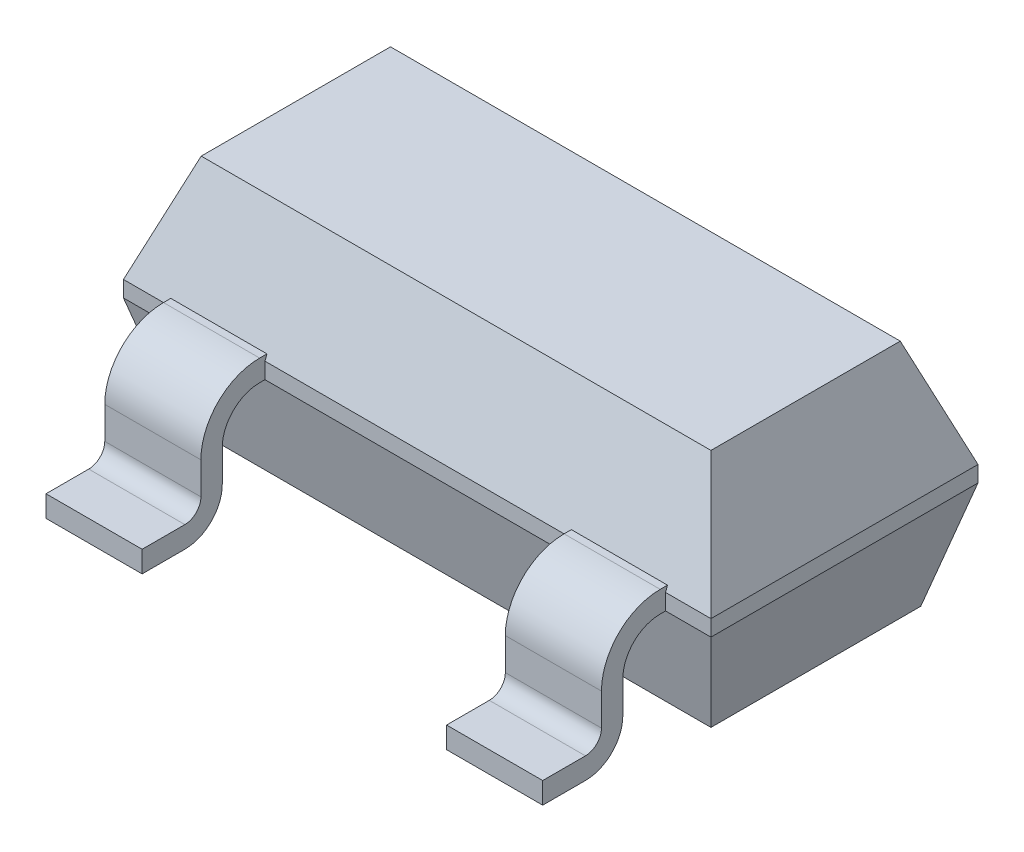
SolidWorks part; units mm, degrees
ref_plane "Front Plane" through (0, 0, 0) normal (0, 0, 1) x (1, 0, 0)
ref_plane "Top Plane" through (0, 0, 0) normal (0, 1, 0) x (1, 0, 0)
ref_plane "Right Plane" through (0, 0, 0) normal (1, 0, 0) x (0, 0, -1)
sketch "Sketch2" plane through (0, 0, 0) normal (0, 1, 0) x (1, 0, 0)
  line L1 (-0.4445, 0.3175) -> (2.3495, 0.3175)
  line L2 (-0.4445, 0.3175) -> (-0.4445, 1.5875)
  line L3 (-0.4445, 1.5875) -> (2.3495, 1.5875)
  line L4 (2.3495, 0.3175) -> (2.3495, 1.5875)
  dimension "D1" = 2.794
  dimension "D2" = 1.27
  dimension "D3" = 0.3175
  dimension "D4" = 0.4445
extrude "Base-Extrude" add sketch "Sketch2" along normal blind 1.0922
chamfer "Chamfer1" distance 0.508 angle 20 4 edges at (2.3495, 1.0922, -0.9525) (0.9525, 1.0922, -1.5875) (-0.4445, 1.0922, -0.9525) (0.9525, 1.0922, -0.3175)
chamfer "Chamfer2" distance 0.508 angle 15 4 edges at (0.9525, 0, -1.5875) (2.3495, 0, -0.9525) (0.9525, 0, -0.3175) (-0.4445, 0, -0.9525)
sketch "Sketch3" plane through (0, 0, 0) normal (1, 0, 0) x (0, 0, -1)
  line L0 (0.1143, 0.3302) -> (0.1143, 0.1778)
  line L3 (-0.0635, 0) -> (-0.2667, 0)
  line L4 (0.2921, 0.508) -> (0.6404, 0.508)
  line L5 (0.3175, 0.508) -> (1.5875, 0.508) construction
  arc A0 (0.2921, 0.508) -> (0.1143, 0.3302) centre (0.2921, 0.3302) ccw
  arc A1 (0.1143, 0.1778) -> (-0.0635, 0) centre (-0.0635, 0.1778) cw
  dimension "D1" = 0.1778
  dimension "D2" = 0.381
  dimension "D3" = 0.5842
extrude "Boss-Extrude-Thin2" add sketch "Sketch3" along normal mid plane 0.4572 thin
pattern_linear "LPattern1" count 2 spacing 1.905 along (1, 0, 0) of "Boss-Extrude-Thin2"
ref_plane "Plane1" through (0.9525, 0, 0) normal (1, 0, 0) x (0, 0, -1)
sketch "Sketch4" plane through (0.9525, 0, 0) normal (1, 0, 0) x (0, 0, -1)
  line L0 (1.6129, 0.508) -> (1.3236, 0.508)
  line L1 (1.7907, 0.3302) -> (1.7907, 0.1778)
  line L2 (1.9685, 0) -> (2.1717, 0)
  line L3 (0.1143, 0.3302) -> (0.1143, 0.1778) construction
  line L5 (0.3175, 0.508) -> (1.5875, 0.508) construction
  line L7 (1.5875, 0.5842) -> (1.5875, 0.508) construction
  arc A0 (1.6129, 0.508) -> (1.7907, 0.3302) centre (1.6129, 0.3302) cw
  arc A1 (1.7907, 0.1778) -> (1.9685, 0) centre (1.9685, 0.1778) ccw
  dimension "D3" = 0.1778
  dimension "D1" = 0.381
  dimension "D2" = 0.5842
extrude "Boss-Extrude-Thin3" add sketch "Sketch4" along normal mid plane 0.4572 thin
sketch "Component_Outline" plane through (0, 0, 0) normal (0, 1, 0) x (1, 0, 0)
  line L0 (2.3495, 0.3175) -> (2.1336, 0.3175)
  line L1 (2.1336, 0.3175) -> (2.1336, -0.2667)
  line L2 (2.1336, -0.2667) -> (1.6764, -0.2667)
  line L3 (1.6764, -0.2667) -> (1.6764, 0.3175)
  line L4 (1.6764, 0.3175) -> (0.2286, 0.3175)
  line L5 (0.2286, 0.3175) -> (0.2286, -0.2667)
  line L6 (0.2286, -0.2667) -> (-0.2286, -0.2667)
  line L7 (-0.2286, -0.2667) -> (-0.2286, 0.3175)
  line L8 (-0.2286, 0.3175) -> (-0.4445, 0.3175)
  line L9 (-0.4445, 1.5875) -> (-0.4445, 0.3175) construction
  line L10 (0.7239, 1.5875) -> (-0.4445, 1.5875)
  line L11 (0.7239, 1.5875) -> (0.7239, 2.1717)
  line L12 (0.7239, 2.1717) -> (1.1811, 2.1717)
  line L13 (1.1811, 2.1717) -> (1.1811, 1.5875)
  line L14 (1.1811, 1.5875) -> (2.3495, 1.5875)
  line L15 (2.3495, 1.5875) -> (2.3495, 0.3175)
  line L16 (-0.4445, 1.5875) -> (-0.4445, 0.3175)
